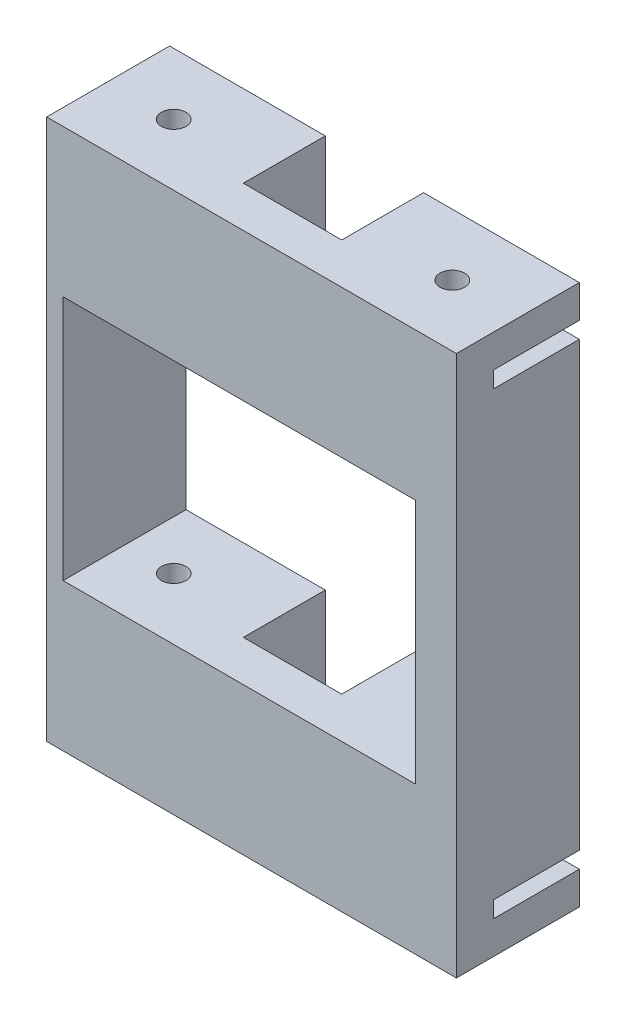
SolidWorks part; units mm, degrees
ref_plane "Alzado" through (0, 0, 0) normal (0, 0, 1) x (1, 0, 0)
ref_plane "Planta" through (0, 0, 0) normal (0, 1, 0) x (1, 0, 0)
ref_plane "Vista lateral" through (0, 0, 0) normal (1, 0, 0) x (0, 0, -1)
sketch "Croquis1" plane through (0, 0, 0) normal (0, 0, 1) x (1, 0, 0)
  line L1 (0, 0) -> (50, 0)
  line L2 (0, 0) -> (0, 66)
  line L3 (0, 66) -> (50, 66)
  line L4 (50, 0) -> (50, 66)
  line L5 (2, 18) -> (45, 18)
  line L6 (2, 18) -> (2, 48)
  line L7 (2, 48) -> (45, 48)
  line L8 (45, 18) -> (45, 48)
  dimension "D1" = 66
  dimension "D2" = 50
  dimension "D3" = 18
  dimension "D4" = 18
  dimension "D5" = 5
  dimension "D6" = 2
extrude "Saliente-Extruir1" add sketch "Croquis1" along normal blind 15
sketch "Croquis2" plane through (0, 0, 0) normal (0, -1, 0) x (1, 0, 0)
  line L0 (25, 15) -> (25, 0) construction
  line L1 (0, 15) -> (50, 15) construction
  line L2 (0, 0) -> (50, 0) construction
  line L3 (31, 5) -> (19, 5) construction
  line L7 (0, 7.5) -> (50, 7.5) construction
  line L8 (0, 15) -> (0, 0) construction
  line L9 (50, 15) -> (50, 0) construction
  line L16 (19, 0) -> (31, 0)
  line L17 (31, 0) -> (31, 10)
  line L18 (31, 10) -> (19, 10)
  line L19 (19, 0) -> (19, 10)
  circle A0 centre (42, 7.5) radius 1.5
  circle A1 centre (8, 7.5) radius 1.5
  point P13 (25, 5)
  dimension "D1" = 3
  dimension "D2" = 17
  dimension "D3" = 10
  dimension "D4" = 12
  dimension "D5" = 7.5
  dimension "D6" = 6
sketch "Croquis3" plane through (0, 0, 0) normal (-1, 0, 0) x (0, 0, 1)
  line L0 (0, 0) -> (0, 4) construction
  line L1 (0, 66) -> (0, 0) construction
  line L2 (0, 66) -> (0, 62) construction
  line L3 (15, 66) -> (15, 0) construction
  line L4 (0, 62) -> (10.5, 62)
  line L5 (0, 62) -> (0, 60)
  line L6 (0, 60) -> (10.5, 60)
  line L7 (10.5, 62) -> (10.5, 60)
  line L8 (0, 4) -> (10.5, 4)
  line L9 (0, 4) -> (0, 6)
  line L10 (0, 6) -> (10.5, 6)
  line L11 (10.5, 4) -> (10.5, 6)
  dimension "D1" = 2
  dimension "D2" = 4.5
  dimension "D3" = 4
extrude "Cortar-Extruir5" cut sketch "Croquis2" against normal through all
extrude "Cortar-Extruir2" cut sketch "Croquis3" against normal blind 12
sketch "Croquis5" plane through (50, 0, 0) normal (1, 0, 0) x (0, 0, -1)
  line L0 (0, 33) -> (-15, 33) construction
  line L1 (0, 0) -> (0, 66) construction
  line L2 (-15, 0) -> (-15, 66) construction
  line L3 (-10.5, 6) -> (-10.5, 4)
  line L4 (0, 60) -> (-10.5, 60)
  line L5 (0, 60) -> (0, 62)
  line L6 (0, 62) -> (-10.5, 62)
  line L7 (-10.5, 60) -> (-10.5, 62)
  line L8 (0, 4) -> (-10.5, 4)
  line L9 (0, 6) -> (0, 4)
  line L10 (0, 6) -> (-10.5, 6)
  dimension "D1" = 4
  dimension "D2" = 2
  dimension "D3" = 4.5
extrude "Cortar-Extruir3" cut sketch "Croquis5" against normal blind 12
